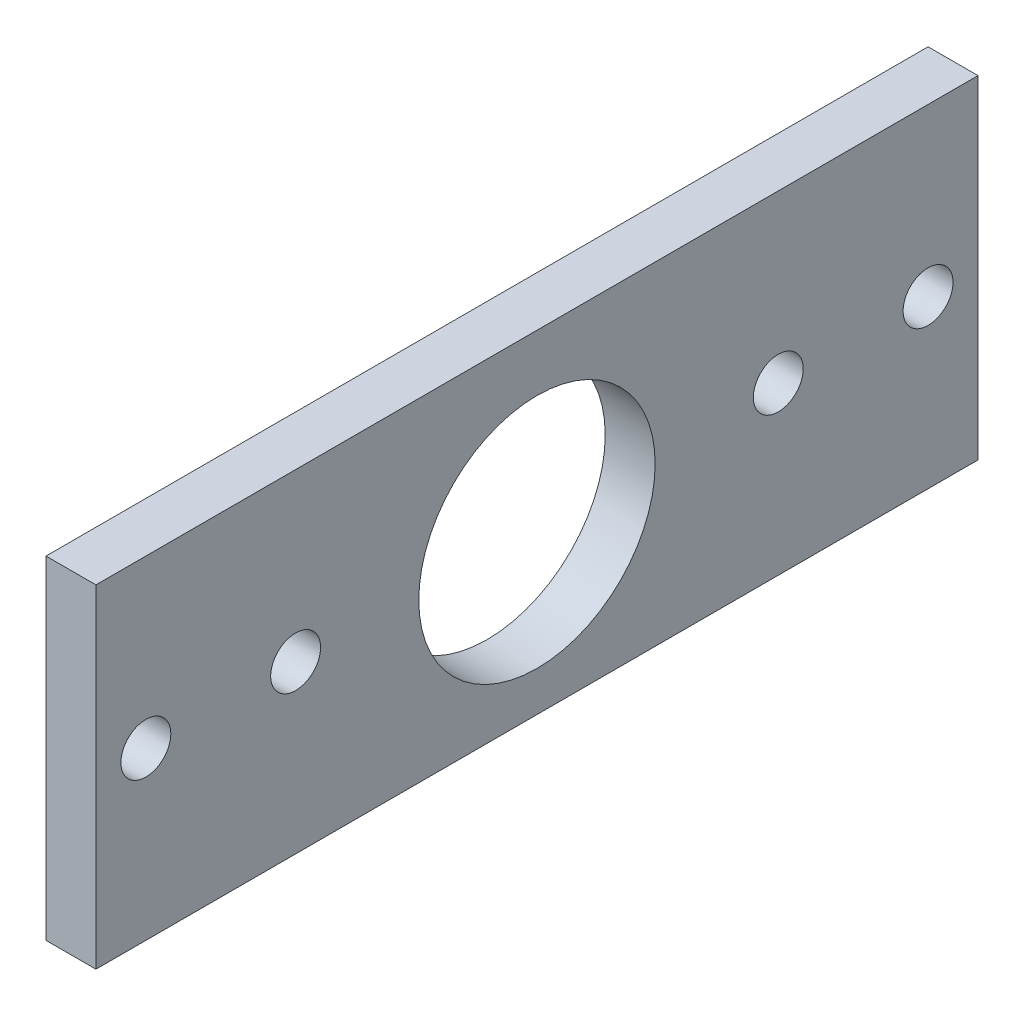
SolidWorks part; units mm, degrees
ref_plane "前视基准面" through (0, 0, 0) normal (0, 0, 1) x (1, 0, 0)
ref_plane "上视基准面" through (0, 0, 0) normal (0, 1, 0) x (1, 0, 0)
ref_plane "右视基准面" through (0, 0, 0) normal (1, 0, 0) x (0, 0, -1)
other "Configuration Table"
sketch "草图1" plane through (0, 0, 0) normal (1, 0, 0) x (0, 0, -1)
  line L0 (26.5, 0) -> (26.5, 20) construction
  line L5 (0, 0) -> (53, 0)
  line L6 (0, 0) -> (0, 20)
  line L7 (0, 20) -> (53, 20)
  line L8 (53, 0) -> (53, 20)
  circle A0 centre (3, 10) radius 1.5
  circle A1 centre (12, 10) radius 1.5
  circle A2 centre (26.5, 9.5) radius 7.1018
  circle A3 centre (41, 10) radius 1.5
  circle A4 centre (50, 10) radius 1.5
  dimension "D7" = 3
  dimension "D8" = 3
  dimension "D1" = 53
  dimension "D2" = 20
  dimension "D3" = 10
  dimension "D4" = 3
  dimension "D5" = 10
  dimension "D6" = 9
  dimension "D9" = 9.5
  dimension "D10" = 26.5
extrude "凸台-拉伸1" add sketch "草图1" along normal blind 3
